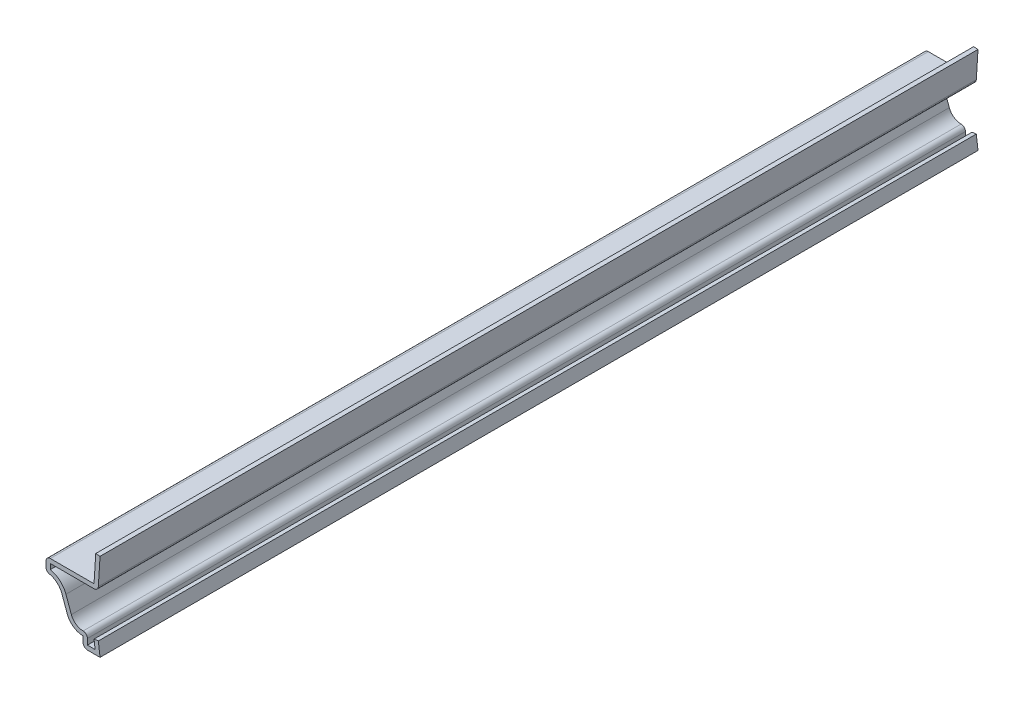
SolidWorks part; units mm, degrees
ref_plane "Front Plane" through (0, 0, 0) normal (0, 0, 1) x (1, 0, 0)
ref_plane "Top Plane" through (0, 0, 0) normal (0, 1, 0) x (1, 0, 0)
ref_plane "Right Plane" through (0, 0, 0) normal (1, 0, 0) x (0, 0, -1)
sketch "Sketch1" plane through (0, 0, 0) normal (0, 0, 1) x (1, 0, 0)
  line L0 (0, 0) -> (0, 20.5741) construction
  line L1 (0, 20.5741) -> (-1.014, 20.6375) construction
  line L2 (-1.014, 20.6375) -> (-1.4109, 14.2875)
  line L3 (-1.4109, 14.2875) -> (-12.7, 14.2875)
  line L4 (-12.7, 14.2875) -> (-12.7, 11.1125)
  line L5 (-8.969, 8.4969) -> (-7.6997, 4.9969)
  line L6 (-3.9688, 2.3813) -> (-3.9688, 0)
  line L7 (-3.9688, 0) -> (0, 0)
  line L8 (0, 0) -> (-0.3969, 3.1501)
  arc A0 (-12.7, 11.1125) -> (-8.969, 8.4969) centre (-12.7, 7.1437) cw
  arc A1 (-7.6997, 4.9969) -> (-3.9688, 2.3813) centre (-3.9688, 6.35) ccw
  point P12 (0, 0)
  point P15 (-2.1127, 14.2875)
  point P16 (0, 0)
  point P17 (-4.2757, 2.1783)
  point P18 (-6.7581, 6.1618)
  point P19 (0, 0)
  point P20 (0, 0)
  dimension "D9" = 3.9688
  dimension "D10" = 3.9688
  dimension "D1" = 14.2875
  dimension "D2" = 6.35
  dimension "D3" = 1.016
  dimension "D4" = 0.3969
  dimension "D5" = 3.175
  dimension "D6" = 12.7
  dimension "D7" = 3.175
  dimension "D8" = 3.9688
  dimension "D11" = 2.3813
  dimension "D12" = 0.3969
extrude "Extrude-Thin1" add sketch "Sketch1" against normal blind 206.375 thin thin type one direction reverse wall 1.016
fillet "Fillet1" radius 1.016 5 edges at (-3.9688, 0, -103.1875) (-2.9527, 3.5776, -103.1875) (-12.7, 11.1125, -103.1875) (-12.7, 14.2875, -103.1875) (-0.4564, 13.2715, -103.1875)
